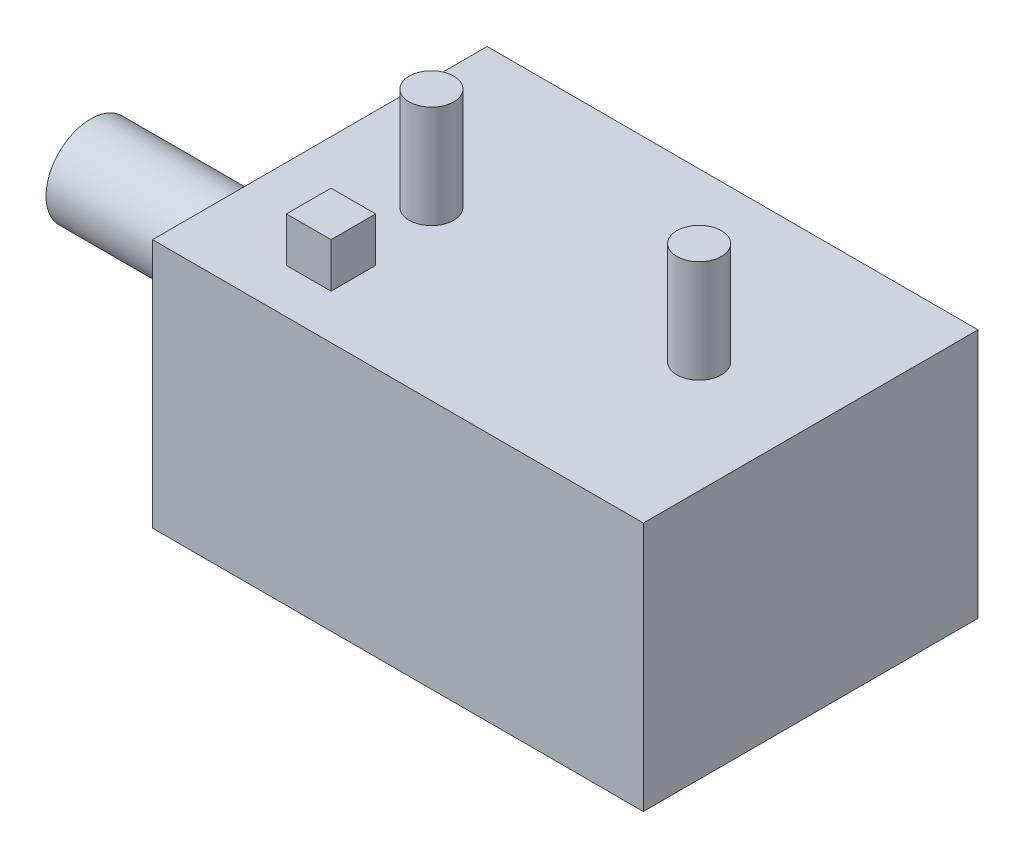
SolidWorks part; units mm, degrees
ref_plane "Front Plane" through (0, 0, 0) normal (0, 0, 1) x (1, 0, 0)
ref_plane "Top Plane" through (0, 0, 0) normal (0, 1, 0) x (1, 0, 0)
ref_plane "Right Plane" through (0, 0, 0) normal (1, 0, 0) x (0, 0, -1)
sketch "Sketch2" plane through (0, 0, 0) normal (0, 1, 0) x (1, 0, 0)
  line L1 (-55, 37.5) -> (55, 37.5)
  line L2 (-55, 37.5) -> (-55, -37.5)
  line L3 (-55, -37.5) -> (55, -37.5)
  line L4 (55, 37.5) -> (55, -37.5)
  line L5 (-55, 37.5) -> (55, -37.5) construction
  line L6 (-55, -37.5) -> (55, 37.5) construction
  point P0 (0, 0)
  dimension "D1" = 110
  dimension "D2" = 75
extrude "Base" add sketch "Sketch2" along normal blind 56
sketch "Sketch3" plane through (0, 56, 0) normal (0, 1, 0) x (1, 0, 0)
  line L0 (55, -37.5) -> (55, 37.5) construction
  circle A0 centre (30, 0) radius 5
  circle A1 centre (-30, 0) radius 5
  dimension "D3" = 10
  dimension "D1" = 25
  dimension "D2" = 60
extrude "HV- Connectors" add sketch "Sketch3" along normal blind 23
sketch "Sketch4" plane through (-55, 0, 0) normal (-1, 0, 0) x (0, 0, 1)
  line L1 (-37.5, 0) -> (37.5, 0) construction
  circle A0 centre (0, 25) radius 10
  dimension "D1" = 20
  dimension "D2" = 25
extrude "LV Connector" add sketch "Sketch4" along normal blind 51.38
sketch "Sketch5" plane through (0, 56, 0) normal (0, 1, 0) x (1, 0, 0)
  line L0 (-55, -37.5) -> (55, -37.5) construction
  line L1 (-35, -17.5) -> (-25, -17.5)
  line L2 (-35, -17.5) -> (-35, -27.5)
  line L3 (-35, -27.5) -> (-25, -27.5)
  line L4 (-25, -17.5) -> (-25, -27.5)
  line L5 (-35, -17.5) -> (-25, -27.5) construction
  line L6 (-35, -27.5) -> (-25, -17.5) construction
  circle A0 centre (-30, 0) radius 5 construction
  point P0 (-30, -22.5)
  point P5 (-30, 0)
  dimension "D1" = 15
  dimension "D2" = 10
  dimension "D3" = 10
extrude "HV+ Connector" add sketch "Sketch5" along normal blind 10
